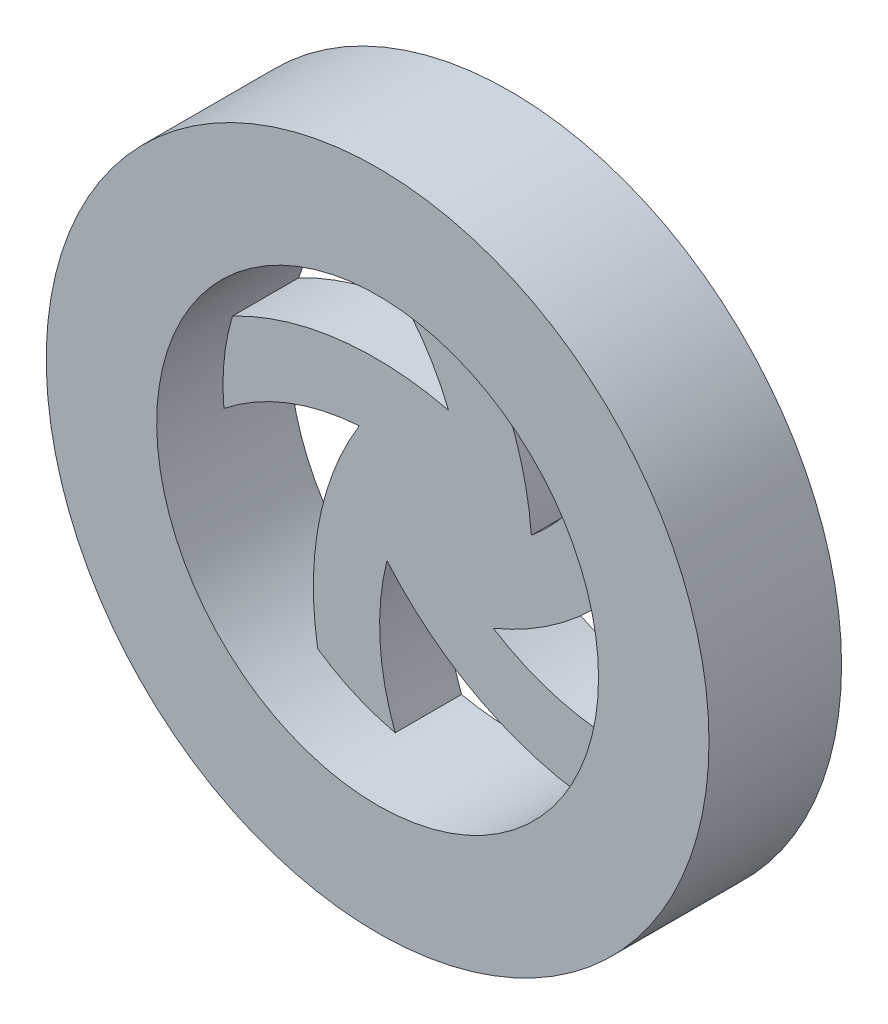
SolidWorks part; units mm, degrees
ref_plane "Front Plane" through (0, 0, 0) normal (0, 0, 1) x (1, 0, 0)
ref_plane "Top Plane" through (0, 0, 0) normal (0, 1, 0) x (1, 0, 0)
ref_plane "Right Plane" through (0, 0, 0) normal (1, 0, 0) x (0, 0, -1)
sketch "Sketch1" plane through (0, 0, 0) normal (0, 0, 1) x (1, 0, 0)
  circle A0 centre (0, 0) radius 75
  circle A1 centre (0, 0) radius 50
  dimension "D1" = 150
  dimension "D2" = 100
extrude "Boss-Extrude1" add sketch "Sketch1" along normal blind 30
sketch "Sketch2" plane through (0, 0, 0) normal (0, 0, -1) x (-1, 0, 0)
  line L0 (0, 0) -> (50, 0) construction
  line L1 (0, 0) -> (-50, 0) construction
  line L2 (0, 0) -> (0, 50) construction
  line L3 (0, 0) -> (0, -50) construction
  circle A0 centre (0, 0) radius 20 construction
  circle A2 centre (0, 0) radius 50 construction
  arc A3 (-37.5828, 32.9778) -> (-47.2343, 16.3988) centre (0, 0) ccw
  arc A4 (1, 49.99) -> (-19.7966, 5.3318) centre (50, 0) ccw
  arc A5 (47.8523, 14.4967) -> (-1.0466, 20.4753) centre (15.4508, -47.5528) ccw
  arc A6 (28.5744, -41.0305) -> (19.1498, 7.3227) centre (-40.4508, -29.3893) ccw
  arc A7 (-30.1924, -39.855) -> (12.8819, -15.9497) centre (-40.4508, 29.3893) ccw
  arc A8 (-47.2343, 16.3988) -> (-11.1884, -17.1801) centre (15.4508, 47.5528) ccw
  arc A9 (19.75, 45.9341) -> (-1.0466, 20.4753) centre (50, 0) ccw
  arc A10 (11.5, 39.2779) -> (-5, 0) centre (50, 0) ccw construction
  arc A11 (49.789, -4.589) -> (19.1498, 7.3227) centre (15.4508, -47.5528) ccw
  arc A12 (11.0213, -48.7702) -> (12.8819, -15.9497) centre (-40.4508, -29.3893) ccw
  arc A13 (-42.9774, -25.5527) -> (-11.1884, -17.1801) centre (-40.4508, 29.3893) ccw
  arc A14 (-37.5828, 32.9778) -> (-19.7966, 5.3318) centre (15.4508, 47.5528) ccw
  arc A15 (19.75, 45.9341) -> (1, 49.99) centre (0, 0) ccw
  arc A16 (1, 49.99) -> (-20, 0) centre (50, 0) ccw construction
  arc A17 (49.789, -4.589) -> (47.8523, 14.4967) centre (0, 0) ccw
  arc A18 (11.0213, -48.7702) -> (28.5744, -41.0305) centre (0, 0) ccw
  arc A19 (-42.9774, -25.5527) -> (-30.1924, -39.855) centre (0, 0) ccw
  circle A20 centre (0, 0) radius 75 construction
  point P4 (0, 0)
  point P27 (0, 0)
  point P30 (28.594, -41.0168)
  point P32 (11.0359, -48.7669)
  point P33 (-30.1914, -39.8557)
  point P36 (-42.9767, -25.5539)
  point P46 (0, 0)
  circle M23 centre (0, 0) radius 50
  dimension "D1" = 40
  dimension "D2" = 70
  dimension "D3" = 55
  dimension "D4" = 11.0213
  dimension "D5" = 15.4508
extrude "Boss-Extrude2" add sketch "Sketch2" against normal blind 15 contours A14 A8 A13 A7 A12 A6 A11 A5 A9 A4 M23
